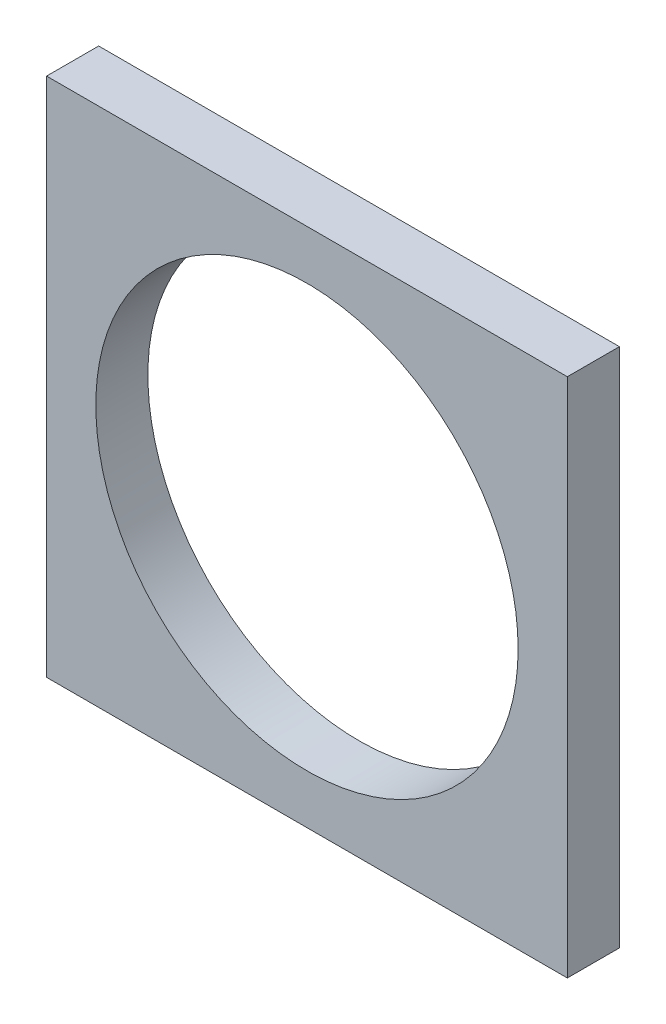
SolidWorks part; units mm, degrees
ref_plane "Front Plane" through (0, 0, 0) normal (0, 0, 1) x (1, 0, 0)
ref_plane "Top Plane" through (0, 0, 0) normal (0, 1, 0) x (1, 0, 0)
ref_plane "Right Plane" through (0, 0, 0) normal (1, 0, 0) x (0, 0, -1)
sketch "Sketch1" plane through (0, 0, 0) normal (0, 0, 1) x (1, 0, 0)
  line L1 (-63.5, 63.5) -> (63.5, 63.5)
  line L2 (-63.5, 63.5) -> (-63.5, -63.5)
  line L3 (-63.5, -63.5) -> (63.5, -63.5)
  line L4 (63.5, 63.5) -> (63.5, -63.5)
  line L5 (-63.5, 63.5) -> (63.5, -63.5) construction
  line L6 (-63.5, -63.5) -> (63.5, 63.5) construction
  point P0 (0, 0)
  dimension "D1" = 127
  dimension "D2" = 127
extrude "Boss-Extrude1" add sketch "Sketch1" along normal blind 12.7
sketch "Sketch2" plane through (0, 0, 12.7) normal (0, 0, 1) x (1, 0, 0)
  circle A0 centre (0, 0) radius 51.5
  dimension "D1" = 103
extrude "Cut-Extrude1" cut sketch "Sketch2" against normal up to next
